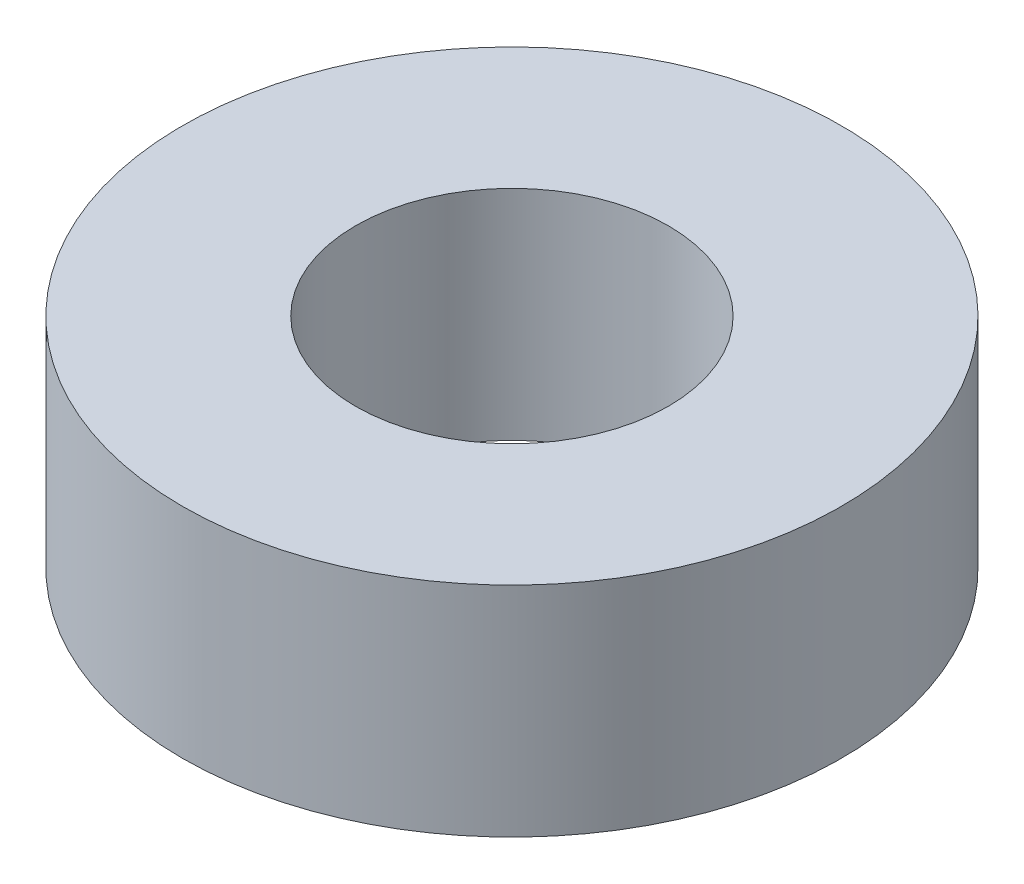
SolidWorks part; units mm, degrees
ref_plane "Alzado" through (0, 0, 0) normal (0, 0, 1) x (1, 0, 0)
ref_plane "Planta" through (0, 0, 0) normal (0, 1, 0) x (1, 0, 0)
ref_plane "Vista lateral" through (0, 0, 0) normal (1, 0, 0) x (0, 0, -1)
sketch "Croquis2" plane through (0, 0, 0) normal (0, 1, 0) x (1, 0, 0)
  circle A0 centre (0, 0) radius 22.65
  circle A1 centre (0, 0) radius 10.75
  dimension "D1" = 45.3
  dimension "D2" = 21.5
extrude "Saliente-Extruir1" add sketch "Croquis2" along normal blind 15
